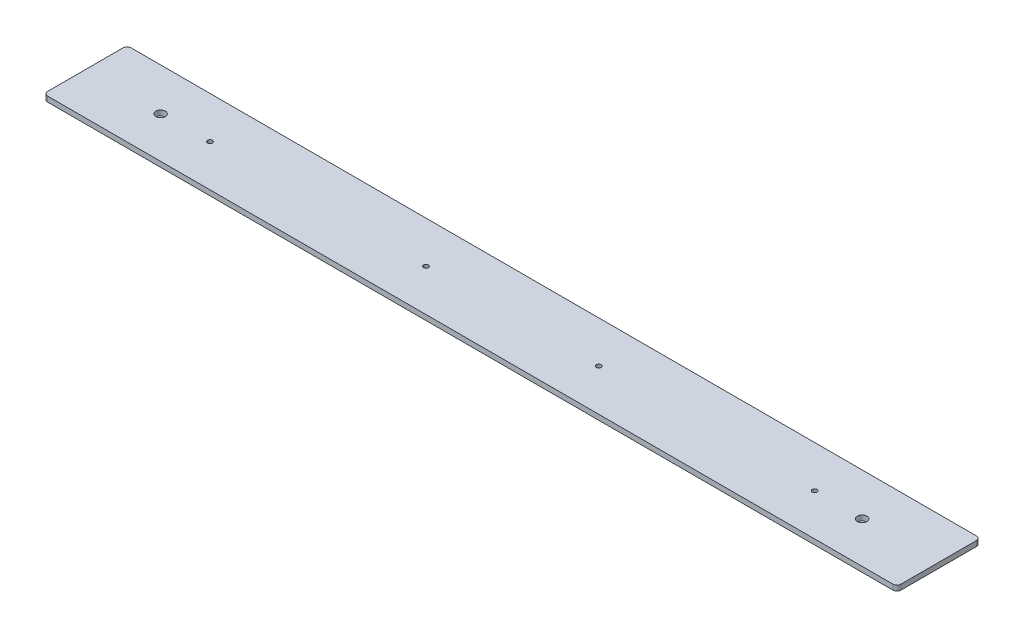
SolidWorks part; units mm, degrees
ref_plane "Front Plane" through (0, 0, 0) normal (0, 0, 1) x (1, 0, 0)
ref_plane "Top Plane" through (0, 0, 0) normal (0, 1, 0) x (1, 0, 0)
ref_plane "Right Plane" through (0, 0, 0) normal (1, 0, 0) x (0, 0, -1)
sketch "Sketch1" plane through (0, 0, 0) normal (0, 1, 0) x (1, 0, 0)
  line L1 (-259.5563, -25.4) -> (259.5562, -25.4)
  line L2 (-259.5563, -25.4) -> (-259.5563, 25.4)
  line L3 (-259.5563, 25.4) -> (259.5562, 25.4)
  line L4 (259.5562, -25.4) -> (259.5562, 25.4)
  line L5 (-259.5563, -25.4) -> (259.5562, 25.4) construction
  line L6 (-259.5563, 25.4) -> (259.5562, -25.4) construction
  point P0 (0, 0)
  dimension "D1" = 519.1125
  dimension "D2" = 50.8
extrude "Boss-Extrude1" add sketch "Sketch1" along normal blind 3.175
fillet "Fillet1" radius 2.54 4 edges at (-259.5563, 1.5875, -25.4) (-259.5563, 1.5875, 25.4) (259.5562, 1.5875, -25.4) (259.5562, 1.5875, 25.4)
hole_wizard "#4 Clearance Hole1" positions "Sketch2" profile "Sketch3" hole size "#4" standard "ANSI Inch" end condition through all
sketch "Sketch2" plane through (0, 3.175, 0) normal (0, 1, 0) x (1, 0, 0)
  point P0 (184.1103, 0)
  point P3 (52.7447, 0)
  point P6 (-52.3478, 0)
  point P9 (-183.7134, 0)
sketch "Sketch3" plane through (184.1103, 3.175, 0) normal (1, 0, 0) x (0, 0, 1)
  line L0 (0, 0) -> (0, 3.175)
  line L1 (0, 3.175) -> (1.4732, 3.175)
  line L2 (1.4732, 3.175) -> (1.4732, 0)
  line L5 (1.4732, 0) -> (0, 0)
  line L11 (0, -6.35) -> (0, 107.95) construction
  dimension "Thru Hole Dia." = 2.9464
  dimension "Thru Hole Depth" = 3.175
hole_wizard "#1 (0.228) Diameter Hole1" positions "Sketch4" profile "Sketch5" hole size "#1" standard "ANSI Inch" end condition through all
sketch "Sketch4" plane through (0, 3.175, 0) normal (0, 1, 0) x (1, 0, 0)
  point P0 (213.36, -0.3869)
  point P3 (-213.36, -0.3869)
sketch "Sketch5" plane through (213.36, 3.175, 0.3869) normal (1, 0, 0) x (0, 0, 1)
  line L0 (0, 0) -> (0, 3.175)
  line L1 (0, 3.175) -> (2.8956, 3.175)
  line L2 (2.8956, 3.175) -> (2.8956, 0)
  line L5 (2.8956, 0) -> (0, 0)
  line L11 (0, -6.35) -> (0, 107.95) construction
  dimension "Thru Hole Dia." = 5.7912
  dimension "Thru Hole Depth" = 3.175
